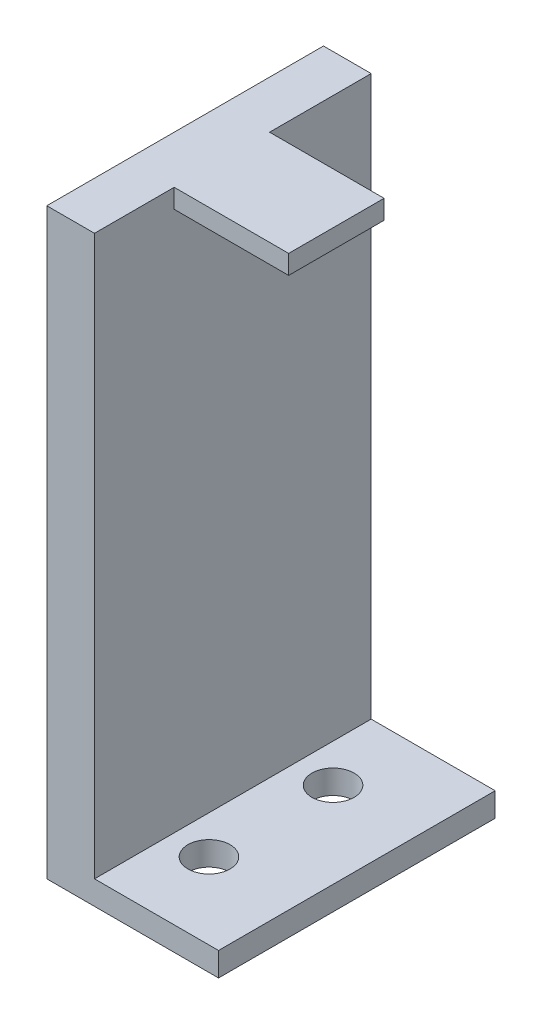
SolidWorks part; units mm, degrees
ref_plane "Front Plane" through (0, 0, 0) normal (0, 0, 1) x (1, 0, 0)
ref_plane "Top Plane" through (0, 0, 0) normal (0, 1, 0) x (1, 0, 0)
ref_plane "Right Plane" through (0, 0, 0) normal (1, 0, 0) x (0, 0, -1)
sketch "Sketch1" plane through (0, 0, 0) normal (0, 1, 0) x (1, 0, 0)
  line L1 (0, 0) -> (-22.86, 0)
  line L2 (0, 0) -> (0, 36.83)
  line L3 (0, 36.83) -> (-22.86, 36.83)
  line L4 (-22.86, 0) -> (-22.86, 36.83)
  dimension "D1" = 36.83
  dimension "D2" = 22.86
extrude "Boss-Extrude1" add sketch "Sketch1" along normal blind 3.175
sketch "Sketch3" plane through (0, 3.175, 0) normal (0, 1, 0) x (1, 0, 0)
  line L0 (-22.86, 0) -> (0, 0) construction
  line L1 (-22.86, 36.83) -> (-16.51, 36.83)
  line L2 (-22.86, 36.83) -> (-22.86, 0)
  line L3 (-22.86, 0) -> (-16.51, 0)
  line L4 (-16.51, 36.83) -> (-16.51, 0)
  dimension "D1" = 6.35
extrude "Boss-Extrude2" add sketch "Sketch3" along normal blind 74.422
sketch "Sketch4" plane through (-16.51, 0, 0) normal (1, 0, 0) x (0, 0, -1)
  line L0 (0, 77.597) -> (36.83, 77.597) construction
  line L1 (10.6066, 77.597) -> (23.3066, 77.597)
  line L2 (10.6066, 77.597) -> (10.6066, 75.057)
  line L3 (10.6066, 75.057) -> (23.3066, 75.057)
  line L4 (23.3066, 77.597) -> (23.3066, 75.057)
  dimension "D1" = 12.7
  dimension "D2" = 2.54
extrude "Boss-Extrude3" add sketch "Sketch4" along normal blind 15.24
hole_wizard "#2 (0.221) Diameter Hole1" positions "Sketch5" profile "Sketch6" hole size "#2" standard "ANSI Inch" end condition up to next
sketch "Sketch5" plane through (0, 0, 0) normal (0, -1, 0) x (-1, 0, 0)
  line L0 (11.43, 36.83) -> (11.43, 0)
  line L1 (0, 36.83) -> (22.86, 36.83) construction
  line L2 (22.86, 0) -> (0, 0) construction
  point P8 (11.43, 26.67)
  point P10 (11.43, 10.16)
  dimension "D1" = 10.16
  dimension "D2" = 10.16
sketch "Sketch6" plane through (-11.43, 0, -10.16) normal (1, 0, 0) x (0, 0, -1)
  line L0 (0, 0) -> (0, 3.175)
  line L1 (0, 3.175) -> (2.8067, 3.175)
  line L2 (2.8067, 3.175) -> (2.8067, 0)
  line L5 (2.8067, 0) -> (0, 0)
  line L11 (0, -6.35) -> (0, 107.95) construction
  dimension "Thru Hole Dia." = 5.6134
  dimension "Thru Hole Depth" = 3.175
ref_plane "Plane1" through (0, 0, -18.415) normal (0, 0, 1) x (1, 0, 0)
